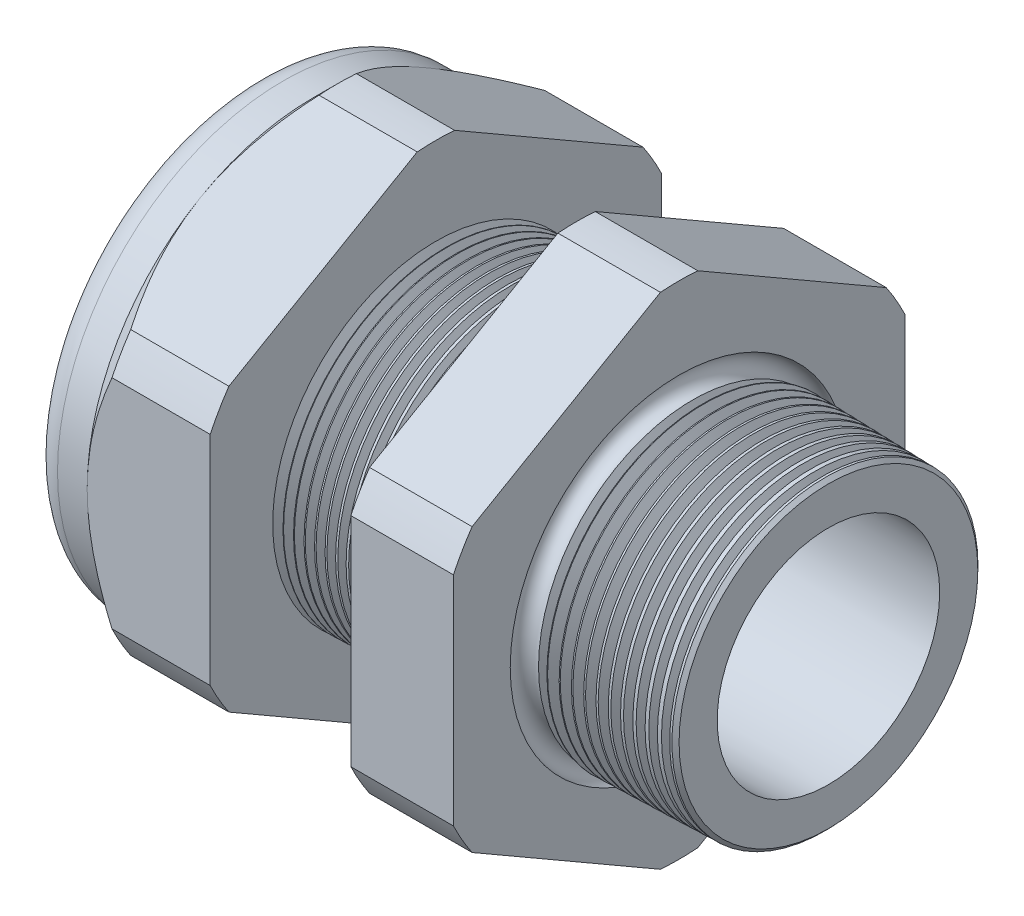
SolidWorks part; units mm, degrees
ref_plane "Front Plane" through (0, 0, 0) normal (0, 0, 1) x (1, 0, 0)
ref_plane "Top Plane" through (0, 0, 0) normal (0, 1, 0) x (1, 0, 0)
ref_plane "Right Plane" through (0, 0, 0) normal (1, 0, 0) x (0, 0, -1)
sketch "Sketch10" plane through (0, 0, 0) normal (0, 0, 1) x (1, 0, 0)
  line L0 (0, 0) -> (-115.3565, 0) construction
  line L1 (-38.862, 9.017) -> (-25.662, 9.017)
  line L2 (3.048, 8.1382) -> (3.048, 11.1862)
  line L3 (-7.874, 11.4722) -> (3.048, 11.1862)
  line L4 (-7.874, 33.02) -> (-7.874, 11.4722)
  line L5 (-7.874, 33.02) -> (-15.374, 33.02)
  line L6 (-15.374, 33.02) -> (-15.374, 11.6686)
  line L7 (-25.662, 11.938) -> (-15.374, 11.6686)
  line L8 (-25.662, 11.938) -> (-25.662, 33.02)
  line L9 (-25.662, 33.02) -> (-34.662, 33.02)
  line L10 (-34.662, 33.02) -> (-34.662, 16.51)
  line L11 (-34.662, 16.51) -> (-38.862, 16.51)
  line L12 (-38.862, 16.51) -> (-38.862, 9.017)
  line L13 (-25.662, 9.017) -> (3.048, 8.1382)
  dimension "D1" = 41.91
  dimension "D2" = 18.034
  dimension "D3" = 1.5
  dimension "D4" = 3.048
  dimension "A" = 23.876
  dimension "D6" = 33.02
  dimension "D8" = 66.04
  dimension "D9" = 4.2
  dimension "D10" = 9
  dimension "D11" = 7.5
  dimension "D" = 10.922
revolve "Revolve2" add sketch "Sketch10" angle 360 about L0
sketch "Sketch12" plane through (-34.662, 0, 0) normal (-1, 0, 0) x (0, 0, 1)
  line L1 (-1.3666, 18.2751) -> (-15.1434, 10.3211)
  line L2 (-16.51, 7.954) -> (-16.51, -7.954)
  line L3 (-15.1434, -10.3211) -> (-1.3666, -18.2751)
  line L4 (1.3666, -18.2751) -> (15.1434, -10.3211)
  line L5 (16.51, -7.954) -> (16.51, 7.954)
  line L6 (15.1434, 10.3211) -> (1.3666, 18.2751)
  circle A0 centre (0, 0) radius 16.51 construction
  arc A1 (1.3666, 18.2751) -> (-1.3666, 18.2751) centre (0, 0) ccw
  arc A2 (-15.1434, 10.3211) -> (-16.51, 7.954) centre (0, 0) ccw
  arc A3 (-16.51, -7.954) -> (-15.1434, -10.3211) centre (0, 0) ccw
  arc A4 (-1.3666, -18.2751) -> (1.3666, -18.2751) centre (0, 0) ccw
  arc A5 (15.1434, -10.3211) -> (16.51, -7.954) centre (0, 0) ccw
  arc A6 (16.51, 7.954) -> (15.1434, 10.3211) centre (0, 0) ccw
  dimension "D2" = 36.6522
  dimension "D1" = 33.02
extrude "Cut-Extrude2" cut sketch "Sketch12" against normal through all flip side to cut
fillet "Fillet4" radius 2.032 1 edges at (-38.862, 0, -16.51)
sketch "Sketch19" plane through (-34.662, 0, 0) normal (-1, 0, 0) x (0, 0, 1)
  line L0 (16.51, 0) -> (16.51, 7.954) construction
  circle A0 centre (0, 0) radius 16.51
extrude "Cut-Extrude3" cut sketch "Sketch19" against normal blind 3.998 draft 45 flip side to cut
chamfer "Chamfer1" distance 0.254 angle 45 1 edges at (3.048, 0, -11.1862)
sketch "Sketch21" plane through (-38.862, 0, 0) normal (-1, 0, 0) x (0, 0, 1)
  circle A0 centre (0, 0) radius 9.017
  circle A2 centre (0, 0) radius 9.017 construction
extrude "plug" add sketch "Sketch21" against normal blind 8.89 separate body
sketch "Sketch22" plane through (-38.862, 0, 0) normal (-1, 0, 0) x (0, 0, 1)
  circle A0 centre (0, 0) radius 8.763
  circle A1 centre (0, 0) radius 9.017 construction
  dimension "D1" = 0.254
extrude "Cut-Extrude4" cut sketch "Sketch22" against normal blind 0.508
sketch "Sketch27" plane through (-38.354, 0, 0) normal (-1, 0, 0) x (0, 0, 1)
  line L0 (-4.3624, 0) -> (4.3624, 0) construction
  circle A0 centre (-6.2128, 0) radius 2.54
  circle A1 centre (0, 0) radius 8.763 construction
  dimension "D1" = 0.0102
  dimension "holedia" = 5.08
extrude "plugholes" cut sketch "Sketch27" against normal through all
pattern_circular "CirPattern1" count 3 over 360 about axis through (0, 0, 0) along (1, 0, 0) of "plugholes"
sketch "Sketch28" [suppressed] plane through (-29.464, 0, 0) normal (-1, 0, 0) x (0, 0, 1)
  circle A0 centre (0, 0) radius 0.762
  dimension "midholedia" = 5.08
extrude "midhole" [suppressed] cut sketch "Sketch28" against normal through all
sketch "Sketch29" plane through (0, 0, 0) normal (0, 0, 1) x (1, 0, 0)
  line L0 (-25.662, 11.938) -> (-24.929, 11.9188)
  line L1 (-15.374, 11.6686) -> (-25.662, 11.938) construction
  line L2 (-24.929, 11.9188) -> (-25.3121, 11.2936)
  line L3 (-25.3121, 11.2936) -> (-25.662, 11.938)
  dimension "D1" = 60
  dimension "D2" = 60
  dimension "D3" = 0.635
revolve "Cut-Revolve1" cut sketch "Sketch29" angle 360 about axis through (0, 0, 0) along (-1, 0, 0)
pattern_linear "LPattern1" count 14 spacing 0.762 along (1, 0, 0) of "Cut-Revolve1"
sketch "Sketch30" plane through (0, 0, 0) normal (0, 0, 1) x (1, 0, 0)
  line L0 (-7.874, 11.4722) -> (-6.9944, 11.4492)
  line L1 (-7.874, 18.2751) -> (-7.874, 10.3211) construction
  line L2 (2.7941, 11.1929) -> (-7.874, 11.4722) construction
  line L3 (-6.9944, 11.4492) -> (-7.4542, 10.6989)
  line L4 (-7.4542, 10.6989) -> (-7.874, 11.4722)
  dimension "D1" = 60
  dimension "D2" = 60
  dimension "D3" = 0.762
revolve "Cut-Revolve2" cut sketch "Sketch30" angle 360 about axis through (0, 0, 0) along (-1, 0, 0)
pattern_linear "LPattern2" count 12 spacing 0.889 along (1, 0, 0) of "Cut-Revolve2"
sketch "Sketch31" [suppressed] plane through (-38.354, 0, 0) normal (-1, 0, 0) x (0, 0, 1)
  line L0 (-1.905, 1.905) -> (1.905, 1.905)
  line L1 (-1.905, -1.905) -> (1.905, -1.905)
  circle A0 centre (0, 0) radius 1.905 construction
  arc A1 (-1.905, 1.905) -> (-1.905, -1.905) centre (-1.905, 0) ccw
  arc A2 (1.905, 1.905) -> (1.905, -1.905) centre (1.905, 0) cw
extrude "Cut-Extrude5" [suppressed] cut sketch "Sketch31" against normal through all
sketch "Sketch32" plane through (0, 0, 0) normal (0, 0, 1) x (1, 0, 0)
  line L0 (-7.874, 18.2751) -> (-7.874, 10.3211) construction
  circle A0 centre (-7.747, 11.4722) radius 0.889
  dimension "D2" = 1.778
  dimension "D1" = 0.127
revolve "Cut-Revolve3" cut sketch "Sketch32" angle 360 about axis through (0, 0, 0) along (-1, 0, 0)
